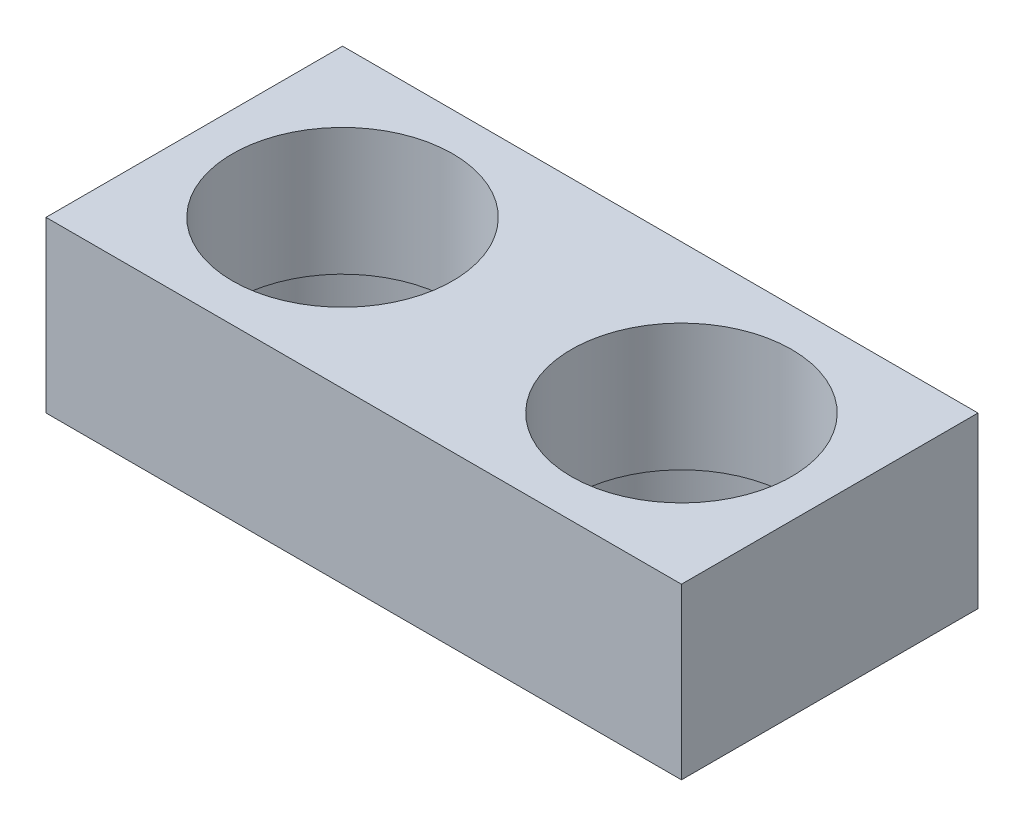
SolidWorks part; units mm, degrees
ref_plane "Alzado" through (0, 0, 0) normal (0, 0, 1) x (1, 0, 0)
ref_plane "Planta" through (0, 0, 0) normal (0, 1, 0) x (1, 0, 0)
ref_plane "Vista lateral" through (0, 0, 0) normal (1, 0, 0) x (0, 0, -1)
sketch "Croquis1" plane through (0, 0, 0) normal (0, 1, 0) x (1, 0, 0)
  line L0 (0, 0) -> (-8, 0) construction
  line L2 (-11.5, -3.5) -> (3.5, -3.5)
  line L3 (-11.5, -3.5) -> (-11.5, 3.5)
  line L4 (-11.5, 3.5) -> (3.5, 3.5)
  line L5 (3.5, -3.5) -> (3.5, 3.5)
  line L6 (-11.5, -3.5) -> (3.5, 3.5) construction
  line L7 (-11.5, 3.5) -> (3.5, -3.5) construction
  circle A0 centre (0, 0) radius 2.6
  circle A1 centre (0, 0) radius 3
  circle A2 centre (-8, 0) radius 2.6
  circle A3 centre (-8, 0) radius 3
  point P7 (-4, 0)
  point P12 (3.5, 0)
  dimension "D1" = 5.2
  dimension "D2" = 6
  dimension "D5" = 8
  dimension "D6" = 3.5
  dimension "D7" = 3.5
extrude "Saliente-Extruir1" add sketch "Croquis1" along normal blind 4 contours L3 L2 L5 L4 | A2 | A0
sketch "Croquis2" plane through (0, 0, 0) normal (0, -1, 0) x (1, 0, 0)
  circle A0 centre (0, 0) radius 3
  circle A1 centre (-8, 0) radius 3
  dimension "D1" = 6
extrude "Cortar-Extruir1" cut sketch "Croquis2" against normal blind 1
